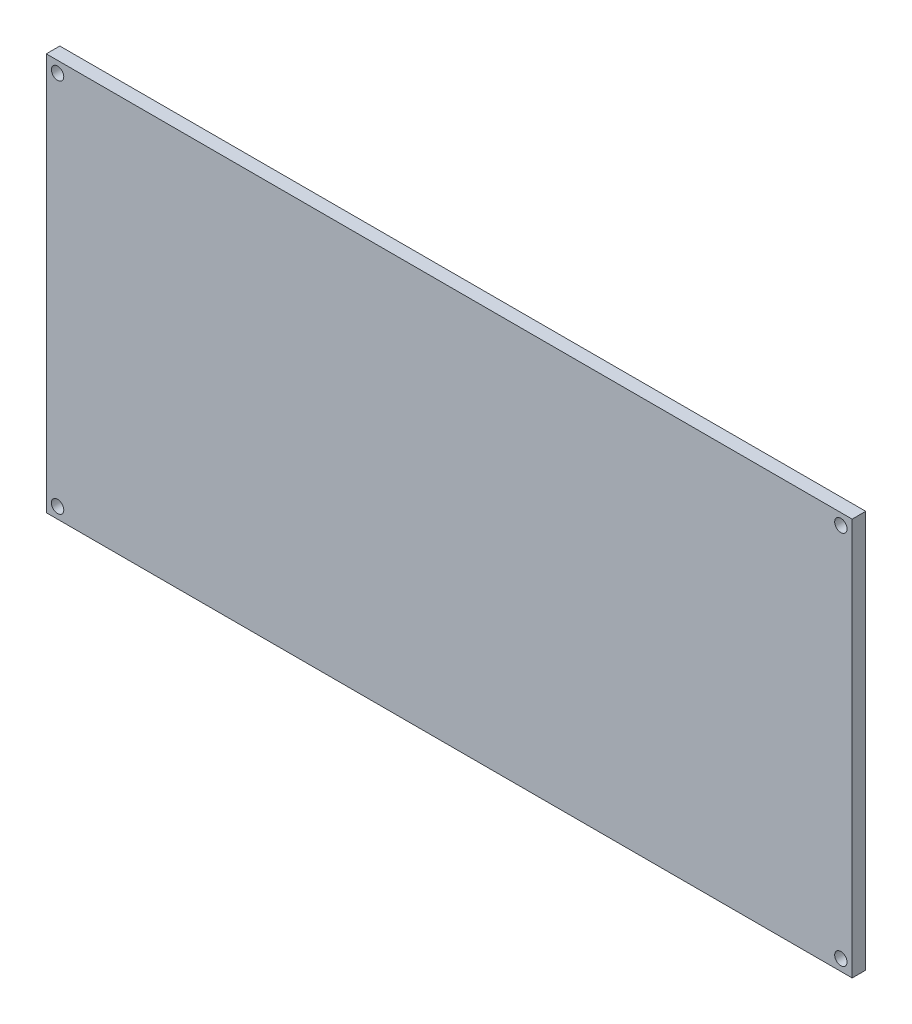
SolidWorks part; units mm, degrees
material "6061-T6 (SS)"
ref_plane "Front Plane" through (0, 0, 0) normal (0, 0, 1) x (1, 0, 0)
ref_plane "Top Plane" through (0, 0, 0) normal (0, 1, 0) x (1, 0, 0)
ref_plane "Right Plane" through (0, 0, 0) normal (1, 0, 0) x (0, 0, -1)
sketch "Sketch1" plane through (0, 0, 0) normal (0, 0, 1) x (1, 0, 0)
  line L0 (0, 0) -> (-94.4, 0) construction
  line L1 (-94.4, -46.55) -> (94.4, -46.55)
  line L2 (-94.4, -46.55) -> (-94.4, 46.55)
  line L3 (-94.4, 46.55) -> (94.4, 46.55)
  line L4 (94.4, -46.55) -> (94.4, 46.55)
  line L5 (-94.4, -46.55) -> (94.4, 46.55) construction
  line L6 (-94.4, 46.55) -> (94.4, -46.55) construction
  line L7 (0, 0) -> (0, 46.55) construction
  circle A0 centre (-91.75, 43.9425) radius 1.45
  circle A1 centre (91.75, 43.9425) radius 1.45
  circle A2 centre (91.75, -43.9425) radius 1.45
  circle A3 centre (-91.75, -43.9425) radius 1.45
  point P0 (0, 0)
  dimension "D3" = 91.75
  dimension "D5" = 2.9
  dimension "D1" = 188.8
  dimension "D2" = 93.1
  dimension "D4" = 43.9425
extrude "Boss-Extrude1" add sketch "Sketch1" along normal blind 3.175
